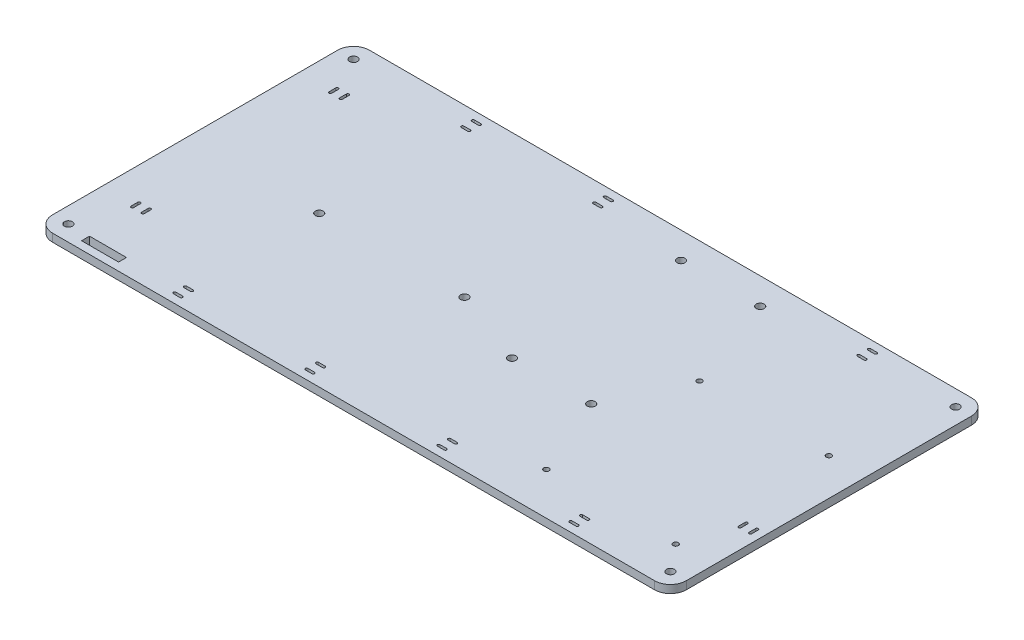
SolidWorks part; units mm, degrees
material "Lasercut ABS"
ref_plane "Front Plane" through (0, 0, 0) normal (0, 0, 1) x (1, 0, 0)
ref_plane "Top Plane" through (0, 0, 0) normal (0, 1, 0) x (1, 0, 0)
ref_plane "Right Plane" through (0, 0, 0) normal (1, 0, 0) x (0, 0, -1)
sketch "Sketch1" plane through (0, 0, 0) normal (0, 1, 0) x (1, 0, 0)
  line L1 (-120, 60) -> (120, 60)
  line L2 (-120, 60) -> (-120, -60)
  line L3 (-120, -60) -> (120, -60)
  line L4 (120, 60) -> (120, -60)
  line L5 (-106, -54) -> (-92, -54)
  line L6 (-106, -54) -> (-106, -57)
  line L7 (-106, -57) -> (-92, -57)
  line L8 (-92, -54) -> (-92, -57)
  point P4 (0, 60)
  point P6 (120, 0)
  dimension "D1" = 240
  dimension "D2" = 120
  dimension "D3" = 3
  dimension "D4" = 14
  dimension "D5" = 3
  dimension "D6" = 14
extrude "Boss-Extrude1" add sketch "Sketch1" along normal blind 3
fillet "Fillet1" radius 6 4 edges at (-120, 1.5, -60) (120, 1.5, -60) (-120, 1.5, 60) (120, 1.5, 60)
sketch "Sketch2" plane through (0, 0, 0) normal (0, 1, 0) x (1, 0, 0)
  circle A0 centre (-114, 54) radius 1.5
  circle A1 centre (114, 54) radius 1.5
  circle A2 centre (-114, -54) radius 1.5
  circle A3 centre (114, -54) radius 1.5
  arc A4 (-114, 60) -> (-120, 54) centre (-114, 54) ccw construction
  arc A5 (-120, -54) -> (-114, -60) centre (-114, -54) ccw construction
  arc A6 (114, -60) -> (120, -54) centre (114, -54) ccw construction
  arc A7 (120, 54) -> (114, 60) centre (114, 54) ccw construction
  dimension "D1" = 3
extrude "Cut-Extrude2" cut sketch "Sketch2" along normal through all
sketch "Sketch3" plane through (0, 3, 0) normal (0, 1, 0) x (1, 0, 0)
  line L0 (-15, -3) -> (-70, -3) construction
  line L1 (-120, 54) -> (-120, -54) construction
  circle A0 centre (-70, -3) radius 1.5
  circle A1 centre (-15, -3) radius 1.5
  point P0 (0, 0)
  dimension "D1" = 3
  dimension "D2" = 50
  dimension "D3" = 55
  dimension "D4" = 3
extrude "Cut-Extrude3" cut sketch "Sketch3" against normal through all
sketch "Sketch4" plane through (0, 3, 0) normal (0, 1, 0) x (1, 0, 0)
  line L0 (114, 60) -> (-114, 60) construction
  line L1 (44, 50) -> (14, 50) construction
  line L2 (44, 50) -> (44, -14) construction
  line L3 (44, -14) -> (14, -14) construction
  line L4 (14, 50) -> (14, -14) construction
  circle A0 centre (44, 50) radius 1.5
  circle A1 centre (14, 50) radius 1.5
  circle A2 centre (44, -14) radius 1.5
  circle A3 centre (14, -14) radius 1.5
  dimension "D5" = 3
  dimension "D1" = 30
  dimension "D2" = 64
  dimension "D3" = 14
  dimension "D4" = 10
extrude "Cut-Extrude4" cut sketch "Sketch4" against normal through all
sketch "Sketch5" plane through (0, 3, 0) normal (0, 1, 0) x (1, 0, 0)
  line L0 (-114, -60) -> (114, -60) construction
  line L1 (106, 14) -> (57, 14) construction
  line L2 (106, 14) -> (106, -44) construction
  line L3 (106, -44) -> (57, -44) construction
  line L4 (57, 14) -> (57, -44) construction
  line L5 (120, -54) -> (120, 54) construction
  circle A0 centre (106, 14) radius 1
  circle A1 centre (106, -44) radius 1
  circle A2 centre (57, -44) radius 1
  circle A3 centre (57, 14) radius 1
  dimension "D1" = 2
  dimension "D2" = 58
  dimension "D3" = 49
  dimension "D4" = 16
  dimension "D5" = 14
extrude "Cut-Extrude5" cut sketch "Sketch5" against normal through all
sketch "Sketch7" plane through (0, 3, 0) normal (0, 1, 0) x (1, 0, 0)
  line L0 (116.5, -23.75) -> (116.5, -26.25) construction
  line L1 (117, -23.75) -> (117, -26.25)
  line L2 (116, -23.75) -> (116, -26.25)
  line L3 (112.5, -23.75) -> (112.5, -26.25) construction
  line L4 (113, -23.75) -> (113, -26.25)
  line L5 (112, -23.75) -> (112, -26.25)
  line L6 (116.5, -25) -> (112.5, -25) construction
  line L7 (81.25, -52.5) -> (78.75, -52.5) construction
  line L8 (81.25, -53) -> (78.75, -53)
  line L9 (81.25, -52) -> (78.75, -52)
  line L10 (81.25, -56.5) -> (78.75, -56.5) construction
  line L11 (81.25, -57) -> (78.75, -57)
  line L12 (81.25, -56) -> (78.75, -56)
  line L13 (80, -52.5) -> (80, -56.5) construction
  line L14 (31.25, -52.5) -> (28.75, -52.5) construction
  line L15 (31.25, -53) -> (28.75, -53)
  line L16 (31.25, -52) -> (28.75, -52)
  line L17 (31.25, -56.5) -> (28.75, -56.5) construction
  line L18 (31.25, -57) -> (28.75, -57)
  line L19 (31.25, -56) -> (28.75, -56)
  line L20 (30, -52.5) -> (30, -56.5) construction
  line L21 (-18.75, -52.5) -> (-21.25, -52.5) construction
  line L22 (-18.75, -53) -> (-21.25, -53)
  line L23 (-18.75, -52) -> (-21.25, -52)
  line L24 (-18.75, -56.5) -> (-21.25, -56.5) construction
  line L25 (-18.75, -57) -> (-21.25, -57)
  line L26 (-18.75, -56) -> (-21.25, -56)
  line L27 (-20, -52.5) -> (-20, -56.5) construction
  line L28 (-68.75, -52.5) -> (-71.25, -52.5) construction
  line L29 (-68.75, -53) -> (-71.25, -53)
  line L30 (-68.75, -52) -> (-71.25, -52)
  line L31 (-68.75, -56.5) -> (-71.25, -56.5) construction
  line L32 (-68.75, -57) -> (-71.25, -57)
  line L33 (-68.75, -56) -> (-71.25, -56)
  line L34 (-70, -52.5) -> (-70, -56.5) construction
  line L35 (13.5504, 0) -> (-62.0868, 0) construction
  line L36 (81.25, 56.5) -> (78.75, 56.5) construction
  line L37 (81.25, 57) -> (78.75, 57)
  line L38 (81.25, 56) -> (78.75, 56)
  line L39 (81.25, 52.5) -> (78.75, 52.5) construction
  line L40 (81.25, 53) -> (78.75, 53)
  line L41 (81.25, 52) -> (78.75, 52)
  line L42 (-18.75, 56.5) -> (-21.25, 56.5) construction
  line L43 (-18.75, 57) -> (-21.25, 57)
  line L44 (-18.75, 56) -> (-21.25, 56)
  line L45 (-18.75, 52.5) -> (-21.25, 52.5) construction
  line L46 (-18.75, 53) -> (-21.25, 53)
  line L47 (-18.75, 52) -> (-21.25, 52)
  line L48 (-68.75, 56.5) -> (-71.25, 56.5) construction
  line L49 (-68.75, 57) -> (-71.25, 57)
  line L50 (-68.75, 56) -> (-71.25, 56)
  line L51 (-68.75, 52.5) -> (-71.25, 52.5) construction
  line L52 (-68.75, 53) -> (-71.25, 53)
  line L53 (-68.75, 52) -> (-71.25, 52)
  line L54 (120, -54) -> (120, 54) construction
  line L55 (114, 60) -> (-114, 60) construction
  line L56 (-103.5, -33.75) -> (-103.5, -36.25) construction
  line L57 (-103, -33.75) -> (-103, -36.25)
  line L58 (-104, -33.75) -> (-104, -36.25)
  line L59 (-107.5, -33.75) -> (-107.5, -36.25) construction
  line L60 (-107, -33.75) -> (-107, -36.25)
  line L61 (-108, -33.75) -> (-108, -36.25)
  line L62 (-103.5, -35) -> (-107.5, -35) construction
  line L63 (-103.5, 41.25) -> (-103.5, 38.75) construction
  line L64 (-103, 41.25) -> (-103, 38.75)
  line L65 (-104, 41.25) -> (-104, 38.75)
  line L66 (-107.5, 41.25) -> (-107.5, 38.75) construction
  line L67 (-107, 41.25) -> (-107, 38.75)
  line L68 (-108, 41.25) -> (-108, 38.75)
  line L69 (-103.5, 40) -> (-107.5, 40) construction
  line L70 (-114, -60) -> (114, -60) construction
  line L71 (-120, 54) -> (-120, -54) construction
  arc A0 (117, -23.75) -> (116, -23.75) centre (116.5, -23.75) ccw
  arc A1 (116, -26.25) -> (117, -26.25) centre (116.5, -26.25) ccw
  arc A2 (113, -23.75) -> (112, -23.75) centre (112.5, -23.75) ccw
  arc A3 (112, -26.25) -> (113, -26.25) centre (112.5, -26.25) ccw
  arc A4 (81.25, -53) -> (81.25, -52) centre (81.25, -52.5) ccw
  arc A5 (78.75, -52) -> (78.75, -53) centre (78.75, -52.5) ccw
  arc A6 (81.25, -57) -> (81.25, -56) centre (81.25, -56.5) ccw
  arc A7 (78.75, -56) -> (78.75, -57) centre (78.75, -56.5) ccw
  arc A8 (31.25, -53) -> (31.25, -52) centre (31.25, -52.5) ccw
  arc A9 (28.75, -52) -> (28.75, -53) centre (28.75, -52.5) ccw
  arc A10 (31.25, -57) -> (31.25, -56) centre (31.25, -56.5) ccw
  arc A11 (28.75, -56) -> (28.75, -57) centre (28.75, -56.5) ccw
  arc A12 (-18.75, -53) -> (-18.75, -52) centre (-18.75, -52.5) ccw
  arc A13 (-21.25, -52) -> (-21.25, -53) centre (-21.25, -52.5) ccw
  arc A14 (-18.75, -57) -> (-18.75, -56) centre (-18.75, -56.5) ccw
  arc A15 (-21.25, -56) -> (-21.25, -57) centre (-21.25, -56.5) ccw
  arc A16 (-68.75, -53) -> (-68.75, -52) centre (-68.75, -52.5) ccw
  arc A17 (-71.25, -52) -> (-71.25, -53) centre (-71.25, -52.5) ccw
  arc A18 (-68.75, -57) -> (-68.75, -56) centre (-68.75, -56.5) ccw
  arc A19 (-71.25, -56) -> (-71.25, -57) centre (-71.25, -56.5) ccw
  arc A20 (81.25, 57) -> (81.25, 56) centre (81.25, 56.5) cw
  arc A21 (78.75, 56) -> (78.75, 57) centre (78.75, 56.5) cw
  arc A22 (81.25, 53) -> (81.25, 52) centre (81.25, 52.5) cw
  arc A23 (78.75, 52) -> (78.75, 53) centre (78.75, 52.5) cw
  arc A24 (-18.75, 57) -> (-18.75, 56) centre (-18.75, 56.5) cw
  arc A25 (-21.25, 56) -> (-21.25, 57) centre (-21.25, 56.5) cw
  arc A26 (-18.75, 53) -> (-18.75, 52) centre (-18.75, 52.5) cw
  arc A27 (-21.25, 52) -> (-21.25, 53) centre (-21.25, 52.5) cw
  arc A28 (-68.75, 57) -> (-68.75, 56) centre (-68.75, 56.5) cw
  arc A29 (-71.25, 56) -> (-71.25, 57) centre (-71.25, 56.5) cw
  arc A30 (-68.75, 53) -> (-68.75, 52) centre (-68.75, 52.5) cw
  arc A31 (-71.25, 52) -> (-71.25, 53) centre (-71.25, 52.5) cw
  arc A32 (-103, -33.75) -> (-104, -33.75) centre (-103.5, -33.75) ccw
  arc A33 (-104, -36.25) -> (-103, -36.25) centre (-103.5, -36.25) ccw
  arc A34 (-107, -33.75) -> (-108, -33.75) centre (-107.5, -33.75) ccw
  arc A35 (-108, -36.25) -> (-107, -36.25) centre (-107.5, -36.25) ccw
  arc A36 (-103, 41.25) -> (-104, 41.25) centre (-103.5, 41.25) ccw
  arc A37 (-104, 38.75) -> (-103, 38.75) centre (-103.5, 38.75) ccw
  arc A38 (-107, 41.25) -> (-108, 41.25) centre (-107.5, 41.25) ccw
  arc A39 (-108, 38.75) -> (-107, 38.75) centre (-107.5, 38.75) ccw
  point P2 (116.5, -25)
  point P7 (112.5, -25)
  point P19 (80, -52.5)
  point P24 (80, -56.5)
  point P35 (30, -52.5)
  point P40 (30, -56.5)
  point P51 (-20, -52.5)
  point P56 (-20, -56.5)
  point P67 (-70, -52.5)
  point P72 (-70, -56.5)
  point P85 (80, 56.5)
  point P92 (80, 52.5)
  point P99 (-20, 56.5)
  point P106 (-20, 52.5)
  point P113 (-70, 56.5)
  point P120 (-70, 52.5)
  point P131 (-103.5, -35)
  point P136 (-107.5, -35)
  point P148 (-103.5, 40)
  point P153 (-107.5, 40)
  dimension "D1" = 3.5
  dimension "D14" = 3.5
  dimension "D2" = 1
  dimension "D3" = 4
  dimension "D4" = 3.5
  dimension "D5" = 1
  dimension "D6" = 4
  dimension "D7" = 3.5
  dimension "D8" = 1
  dimension "D9" = 4
  dimension "D10" = 3
  dimension "D11" = 4
  dimension "D12" = 50
  dimension "D13" = 1
  dimension "D15" = 50
  dimension "D16" = 50
  dimension "D17" = 50
  dimension "D18" = 3
  dimension "D19" = 35
  dimension "D20" = 12
  dimension "D21" = 20
  dimension "D22" = 35
extrude "Cut-Extrude6" cut sketch "Sketch7" against normal through all
